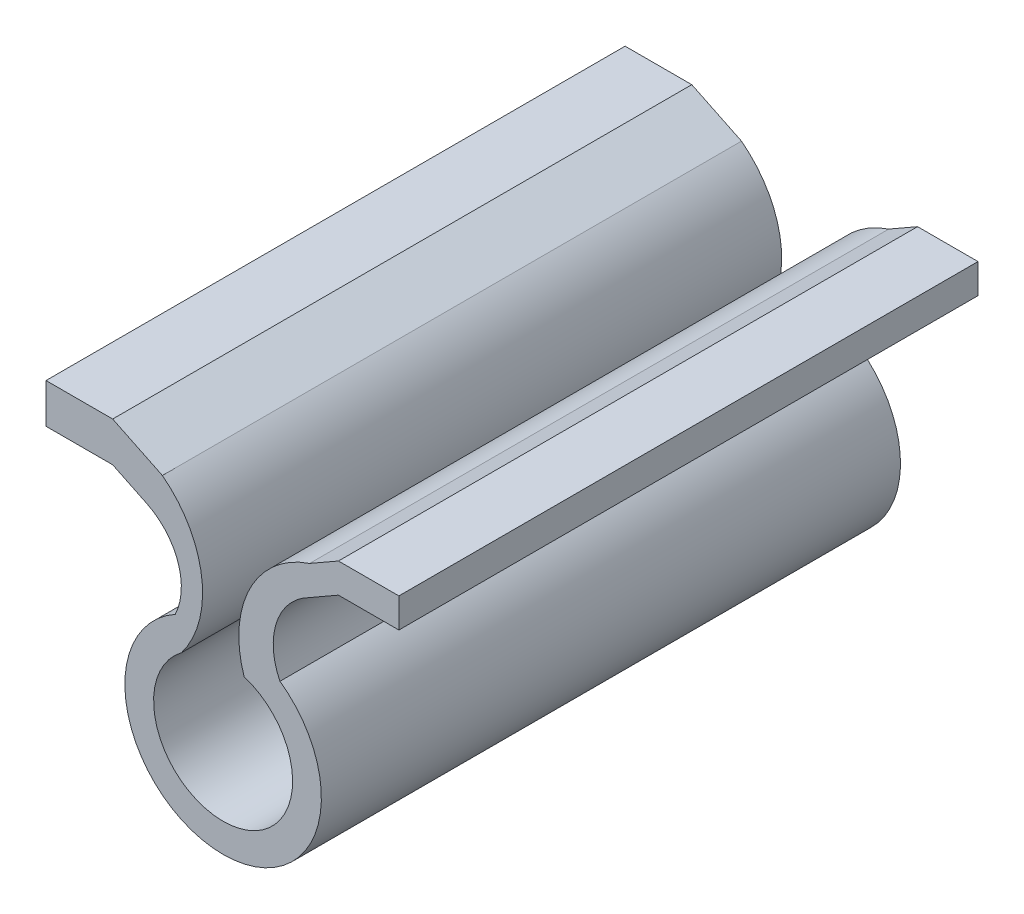
SolidWorks part; units mm, degrees
ref_plane "Front Plane" through (0, 0, 0) normal (0, 0, 1) x (1, 0, 0)
ref_plane "Top Plane" through (0, 0, 0) normal (0, 1, 0) x (1, 0, 0)
ref_plane "Right Plane" through (0, 0, 0) normal (1, 0, 0) x (0, 0, -1)
sketch "Sketch1" plane through (0, 0, 0) normal (0, 0, 1) x (1, 0, 0)
  line L0 (-6.5866, 14.4601) -> (-9.5348, 15.8868)
  line L1 (-9.5348, 15.8868) -> (-15.2917, 15.8868)
  line L2 (-15.2917, 15.8868) -> (-15.2917, 19.3101)
  line L3 (-15.2917, 19.3101) -> (-9.5348, 19.3101)
  line L4 (-9.5348, 19.3101) -> (-5.2443, 17.2338)
  line L5 (7.4659, 14.4601) -> (9.9566, 15.8868)
  line L6 (9.9566, 15.8868) -> (15.1761, 15.8868)
  line L7 (15.1761, 15.8868) -> (15.1761, 18.4396)
  line L8 (15.1761, 18.4396) -> (9.9566, 18.4396)
  line L9 (9.9566, 18.4396) -> (7.4659, 17.0129)
  arc A0 (-4.1339, 7.4075) -> (4.9069, 6.9197) centre (0, 0) ccw
  arc A1 (-4.1339, 7.4075) -> (-6.5866, 14.4601) centre (-8.8866, 9.7074) ccw
  arc A2 (4.9069, 6.9197) -> (7.4659, 14.4601) centre (9.9566, 9.4104) cw
  arc A3 (-3.6066, 4.795) -> (1.8119, 5.7199) centre (0, 0) ccw
  arc A4 (-5.2443, 17.2338) -> (-3.6066, 4.795) centre (-10.6449, 10.1956) cw
  arc A5 (7.4659, 17.0129) -> (1.8119, 5.7199) centre (10.2854, 8.5394) ccw
  dimension "D1" = 12
extrude "Boss-Extrude1" add sketch "Sketch1" against normal blind 50
